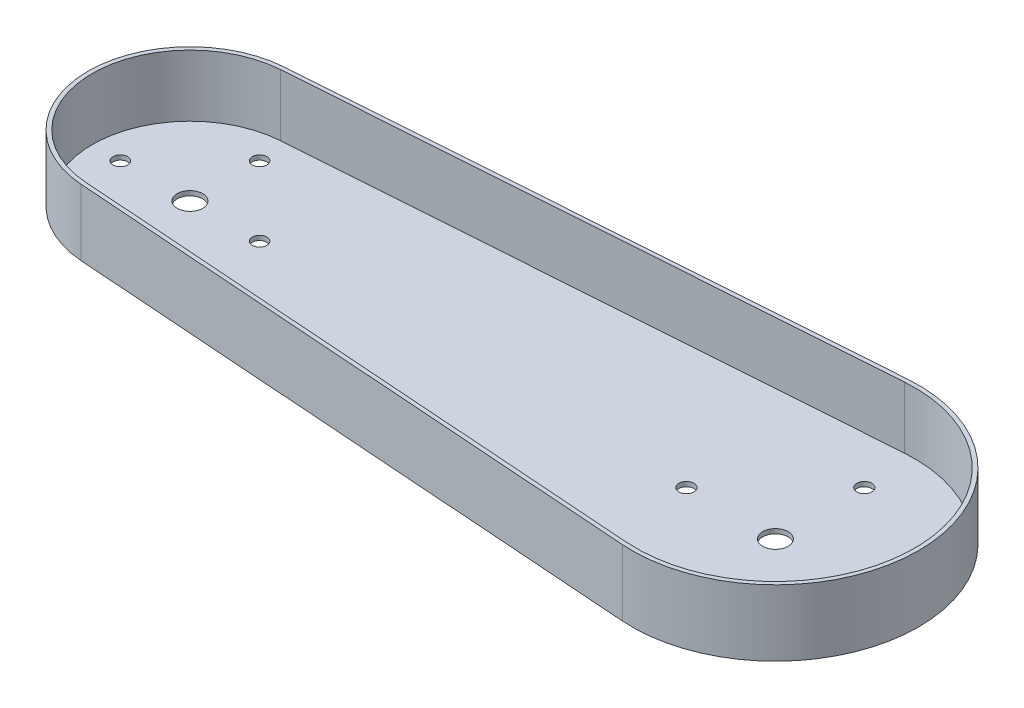
SolidWorks part; units mm, degrees
ref_plane "Front Plane" through (0, 0, 0) normal (0, 0, 1) x (1, 0, 0)
ref_plane "Top Plane" through (0, 0, 0) normal (0, 1, 0) x (1, 0, 0)
ref_plane "Right Plane" through (0, 0, 0) normal (1, 0, 0) x (0, 0, -1)
sketch "Sketch1" plane through (0, 0, 0) normal (0, 1, 0) x (1, 0, 0)
  line L0 (-2.8348, 39.8994) -> (226.01, 56.1584)
  line L1 (-2.8348, -39.8994) -> (226.01, -56.1584)
  line L2 (5, 0) -> (225, 0) construction
  line L3 (0, -5) -> (0, -40) construction
  line L4 (230, -5) -> (230, -56.3) construction
  line L5 (0, 24.5) -> (0, 5) construction
  line L6 (230, 32) -> (230, 5) construction
  circle A0 centre (0, 0) radius 40
  circle A1 centre (230, 0) radius 56.3
  circle A2 centre (0, 0) radius 5
  circle A3 centre (230, 0) radius 5
  circle A4 centre (0, 0) radius 27.35 construction
  circle A5 centre (230, 0) radius 34.95 construction
  circle A6 centre (0, 27.35) radius 2.85
  circle A7 centre (27.35, 0) radius 2.85
  circle A8 centre (0, -27.35) radius 2.85
  circle A9 centre (-27.35, 0) radius 2.85
  circle A10 centre (230, 34.95) radius 2.95
  circle A11 centre (264.95, 0) radius 2.95
  circle A12 centre (230, -34.95) radius 2.95
  circle A13 centre (195.05, 0) radius 2.95
  dimension "D1" = 220
  dimension "D4" = 10
  dimension "D5" = 10
  dimension "D7" = 5.7
  dimension "D8" = 5.9
  dimension "D2" = 51.3
  dimension "D3" = 35
  dimension "D6" = 19.5
  dimension "D9" = 27
extrude "Boss-Extrude1" add sketch "Sketch1" along normal blind 26 contours A1 L0 A0 L1 | A0 A9 A8 A7 A6 A2 | A1 A13 A12 A11 A10 A3
sketch "Sketch2" plane through (0, 26, 0) normal (0, 1, 0) x (1, 0, 0)
  line L8 (-2.7214, -38.3034) -> (226.1234, -54.5625)
  line L9 (226.1234, 54.5625) -> (-2.7214, 38.3034)
  line L10 (-2.7214, -38.3034) -> (226.1234, -54.5625)
  line L11 (226.1234, 54.5625) -> (-2.7214, 38.3034)
  arc A6 (226.1234, -54.5625) -> (226.1234, 54.5625) centre (230, 0) ccw
  arc A7 (-2.7214, 38.3034) -> (-2.7214, -38.3034) centre (0, 0) ccw
  arc A8 (226.1234, -54.5625) -> (226.1234, 54.5625) centre (230, 0) ccw
  arc A9 (-2.7214, 38.3034) -> (-2.7214, -38.3034) centre (0, 0) ccw
  dimension "D1" = 1.6
extrude "Cut-Extrude1" cut sketch "Sketch2" against normal blind 24.2
